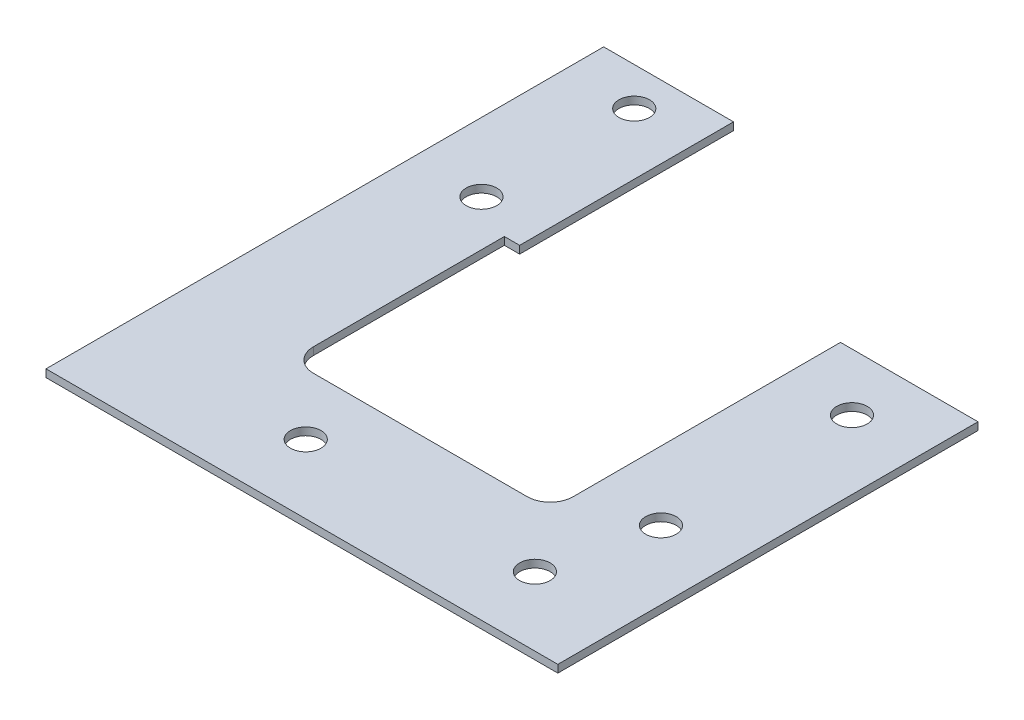
SolidWorks part; units mm, degrees
ref_plane "Front" through (0, 0, 0) normal (0, 0, 1) x (1, 0, 0)
ref_plane "Top" through (0, 0, 0) normal (0, 1, 0) x (1, 0, 0)
ref_plane "Right" through (0, 0, 0) normal (1, 0, 0) x (0, 0, -1)
sketch "Sketch1" plane through (0, 0, 0) normal (0, 1, 0) x (1, 0, 0)
  line L2 (0, 0) -> (0, 40) construction
  line L3 (0, 40) -> (15, 40)
  line L4 (15, 0) -> (15, 40)
  line L5 (0, 20) -> (15, 20) construction
  line L6 (0, 40) -> (-3, 40)
  line L7 (-3, 40) -> (-3, 5)
  line L9 (15, 0) -> (15, -15)
  line L10 (15, -15) -> (-52, -15)
  line L11 (-52, -15) -> (-52, 58)
  line L12 (-52, 58) -> (-37, 58)
  line L13 (-37, 30) -> (-37, 5)
  line L15 (-37, 58) -> (-35, 58)
  line L16 (-35, 58) -> (-35, 30)
  line L17 (-35, 30) -> (-37, 30)
  line L18 (-6, 2) -> (-34, 2)
  circle A0 centre (6, 32.5) radius 2
  circle A1 centre (6, 7.5) radius 2
  circle A2 centre (-43, 53) radius 2
  circle A3 centre (-43, 33) radius 2
  circle A4 centre (-27, -6) radius 2
  circle A5 centre (3, -6) radius 2
  arc A6 (-34, 2) -> (-37, 5) centre (-34, 5) cw
  arc A7 (-3, 5) -> (-6, 2) centre (-6, 5) cw
  dimension "D3" = 4
  dimension "D13" = 4
  dimension "D20" = 3
  dimension "D21" = 3
  dimension "D1" = 40
  dimension "D2" = 15
  dimension "D4" = 25
  dimension "D5" = 3
  dimension "D6" = 15
  dimension "D7" = 15
  dimension "D8" = 37
  dimension "D9" = 2
  dimension "D10" = 2
  dimension "D11" = 30
  dimension "D12" = 73
  dimension "D14" = 20
  dimension "D15" = 9
  dimension "D16" = 30
  dimension "D17" = 9
  dimension "D18" = 25
  dimension "D19" = 9
extrude "Boss-Extrude2" add sketch "Sketch1" along normal blind 1
equation "\"d_racor\"= 11.8"
equation "\"h_alphasense\"= 5"
equation "\"h_chamber\"= 13"
equation "\"d_alphasense\" = 32.4mm"
equation "\"d_chamber\"= 19"
equation "\"h_base\"= 25 - \"h_chamber\" - \"h_alphasense\"-1"
equation "\"d_thread\"= 2.5"
equation "\"length_thread\"=10"
equation "\"clip_thread_hole\" = 4"
equation "\"clip_thread_tap_drill\" = 3.5"
equation "\"length_racor\"= 10"
equation "\"d_pipe\"=8"
equation "\"D3@Sketch1\"=\"clip_thread_hole\""
equation "\"D13@Sketch1\"=\"clip_thread_hole\""
